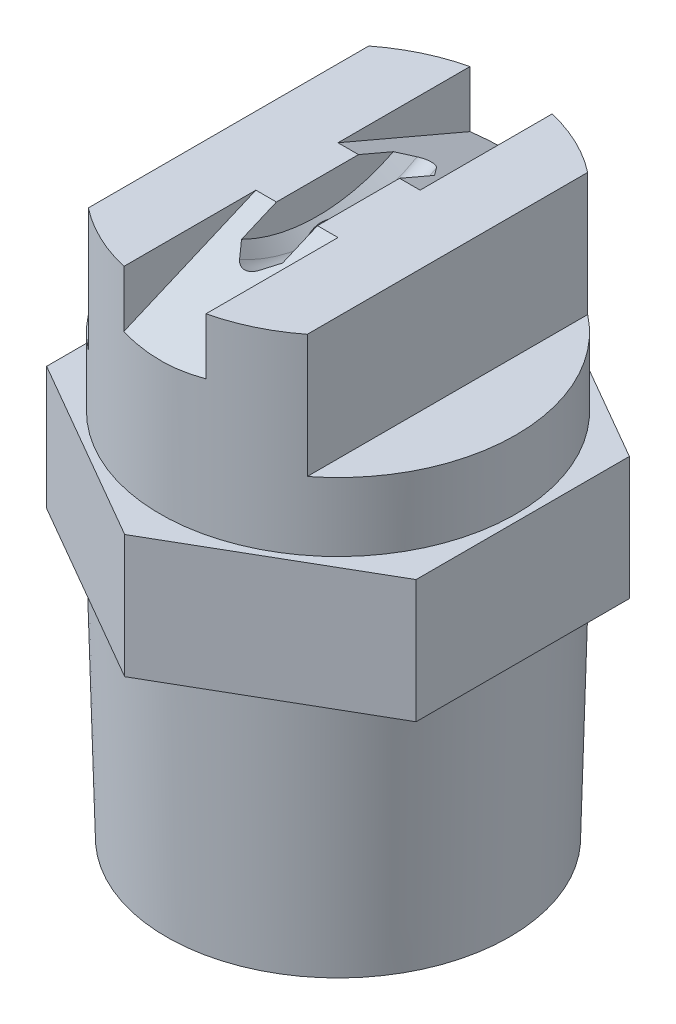
SolidWorks part; units mm, degrees
material "AISI 316 Annealed Stainless Steel Bar (SS)"
ref_plane "Front Plane" through (0, 0, 0) normal (0, 0, 1) x (1, 0, 0)
ref_plane "Top Plane" through (0, 0, 0) normal (0, 1, 0) x (1, 0, 0)
ref_plane "Right Plane" through (0, 0, 0) normal (1, 0, 0) x (0, 0, -1)
sketch "Sketch1" plane through (0, 0, 0) normal (0, 0, 1) x (1, 0, 0)
  line L0 (0, 0) -> (0, 20.5) construction
  line L1 (-3.5, 0) -> (-6.269, 0)
  line L2 (-6.269, 0) -> (-6.5, 9)
  line L3 (-6.5, 9) -> (-6.5, 20.5)
  line L4 (-6.5, 20.5) -> (0, 20.5)
  line L5 (0, 20.5) -> (0, 19.5)
  line L6 (0, 19.5) -> (-2.5, 18.171)
  line L7 (-2.5, 18.171) -> (-2.5, 14.8855)
  line L8 (-2.5, 14.8855) -> (-3.5, 14.8855)
  line L9 (-3.5, 14.8855) -> (-3.5, 0)
  line L10 (-6.5, 9.1579) -> (-6.5, 1.1225) construction
  dimension "D1" = 20.5
  dimension "D2" = 3.5
  dimension "D3" = 6.5
  dimension "D4" = 1.47
  dimension "D5" = 9
  dimension "D6" = 1
  dimension "D7" = 1
revolve "Revolve1" add sketch "Sketch1" angle 360 about L0
ref_plane "Plane1" through (0, 9, 0) normal (0, -1, 0) x (-1, 0, 0)
sketch "Sketch2" plane through (0, 9, 0) normal (0, -1, 0) x (-1, 0, 0)
  line L1 (0, 7.7942) -> (-6.75, 3.8971)
  line L2 (-6.75, 3.8971) -> (-6.75, -3.8971)
  line L3 (-6.75, -3.8971) -> (0, -7.7942)
  line L4 (0, -7.7942) -> (6.75, -3.8971)
  line L5 (6.75, -3.8971) -> (6.75, 3.8971)
  line L6 (6.75, 3.8971) -> (0, 7.7942)
  circle A0 centre (0, 0) radius 6.75 construction
  circle A1 centre (0, 0) radius 3.5 construction
  circle A2 centre (0, 0) radius 3.5
  dimension "D1" = 13.5
extrude "Boss-Extrude1" add sketch "Sketch2" against normal blind 4.5
sketch "Sketch3" plane through (0, 20.5, 0) normal (0, 1, 0) x (1, 0, 0)
  line L1 (4, -9.8795) -> (-4, -9.8795)
  line L2 (4, -9.8795) -> (4, 9.8795)
  line L3 (4, 9.8795) -> (-4, 9.8795)
  line L4 (-4, -9.8795) -> (-4, 9.8795)
  line L5 (4, -9.8795) -> (-4, 9.8795) construction
  line L6 (4, 9.8795) -> (-4, -9.8795) construction
  point P0 (0, 0)
  dimension "D1" = 8
extrude "Cut-Extrude1" cut sketch "Sketch3" against normal blind 4.5 flip side to cut
sketch "Sketch4" plane through (0, 0, 0) normal (1, 0, 0) x (0, 0, -1)
  line L0 (-1.5, 20.5) -> (1.5, 20.5)
  line L1 (-5.1235, 20.5) -> (5.1235, 20.5) construction
  line L2 (-1.5, 20.5) -> (-6.9375, 18.1787)
  line L3 (-6.9375, 18.1787) -> (-6.9375, 21.048)
  line L4 (0, 20.5) -> (0, 25.4303) construction
  line L5 (1.5, 20.5) -> (6.9375, 18.1787)
  line L6 (6.9375, 18.1787) -> (6.9375, 21.048)
  line L7 (-6.9375, 21.048) -> (6.9375, 21.048)
  point P5 (0, 20.5)
  dimension "D1" = 3
extrude "Cut-Extrude2" cut sketch "Sketch4" against normal mid plane 3
sketch "Sketch8" plane through (0, 0, 0) normal (0, 0, 1) x (1, 0, 0)
  line L0 (0, 0) -> (0, 40.4748) construction
  line L3 (-0.75, 19.3) -> (-0.3536, 18.9036)
  line L4 (0.3536, 18.9036) -> (0.75, 19.3)
  line L6 (4, 20.5) -> (1.5, 20.5) construction
  line L7 (0, 25.5) -> (-3.0268, 25.5) construction
  line L8 (-0.75, 19.3) -> (-0.75, 25.5)
  line L9 (-0.75, 25.5) -> (0.75, 25.5)
  line L10 (0.75, 25.5) -> (0.75, 19.3)
  arc A0 (-0.3536, 18.9036) -> (0.3536, 18.9036) centre (0, 19.2571) ccw
  point P9 (0, 18.55)
  dimension "D1" = 0.5
  dimension "D2" = 1.5
  dimension "D3" = 5
  dimension "D4" = 6.2
revolve "Cut-Revolve2" cut sketch "Sketch8" angle 360 about L7
